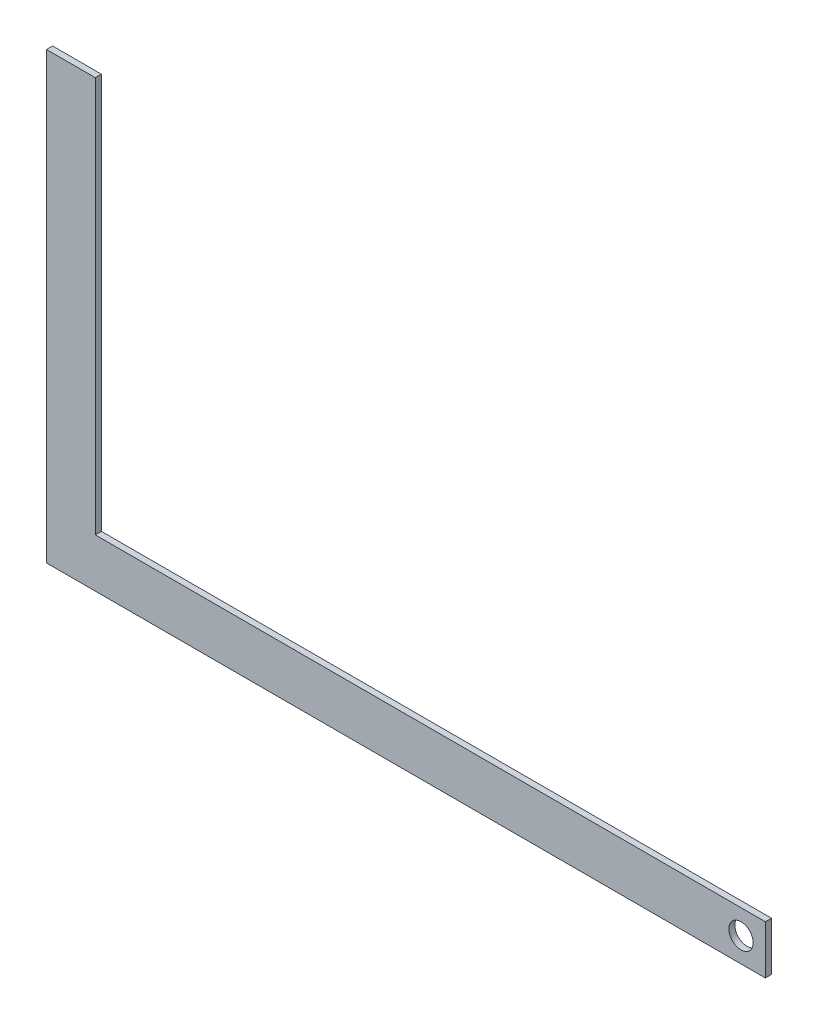
SolidWorks part; units mm, degrees
ref_plane "Front" through (0, 0, 0) normal (0, 0, 1) x (1, 0, 0)
ref_plane "Top" through (0, 0, 0) normal (0, 1, 0) x (1, 0, 0)
ref_plane "Right" through (0, 0, 0) normal (1, 0, 0) x (0, 0, -1)
sketch "Sketch1" plane through (0, 0, 0) normal (0, 0, 1) x (1, 0, 0)
  line L1 (0, 0) -> (374.65, 0)
  line L2 (0, 0) -> (0, 25.4)
  line L3 (0, 25.4) -> (374.65, 25.4)
  line L4 (374.65, 0) -> (374.65, 25.4)
  line L5 (0, 0) -> (374.65, 25.4) construction
  line L6 (0, 25.4) -> (374.65, 0) construction
  circle A0 centre (361.95, 12.7) radius 6.35
  point P4 (187.325, 12.7)
  dimension "D3" = 12.7
  dimension "D1" = 25.4
  dimension "D2" = 374.65
  dimension "D4" = 12.7
extrude "Boss-Extrude1" add sketch "Sketch1" along normal blind 3.175
sketch "Sketch2" plane through (0, 0, 3.175) normal (0, 0, 1) x (1, 0, 0)
  line L1 (0, 25.4) -> (25.4, 25.4)
  line L2 (0, 25.4) -> (0, 231.775)
  line L3 (0, 231.775) -> (25.4, 231.775)
  line L4 (25.4, 25.4) -> (25.4, 231.775)
  line L5 (0, 25.4) -> (25.4, 231.775) construction
  line L6 (0, 231.775) -> (25.4, 25.4) construction
  point P4 (12.7, 128.5875)
  dimension "D1" = 206.375
  dimension "D2" = 25.4
extrude "Boss-Extrude2" add sketch "Sketch2" against normal blind 3.175
